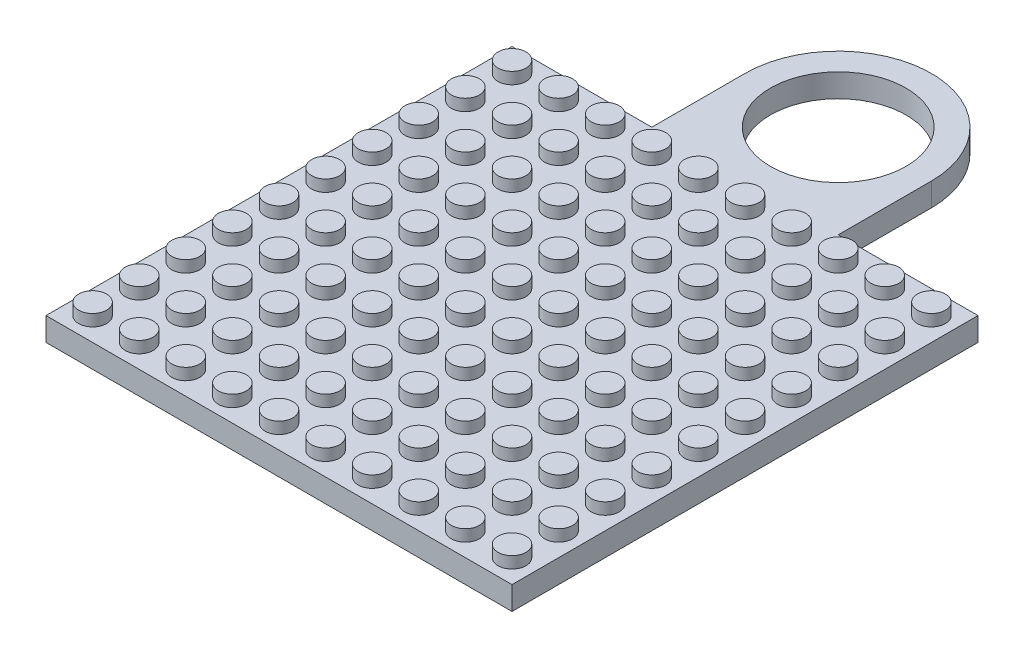
SolidWorks part; units mm, degrees
ref_plane "Front Plane" through (0, 0, 0) normal (0, 0, 1) x (1, 0, 0)
ref_plane "Top Plane" through (0, 0, 0) normal (0, 1, 0) x (1, 0, 0)
ref_plane "Right Plane" through (0, 0, 0) normal (1, 0, 0) x (0, 0, -1)
sketch "Sketch1" plane through (0, 0, 0) normal (0, 1, 0) x (1, 0, 0)
  line L1 (5, -5) -> (-5, -5)
  line L2 (5, -5) -> (5, 5)
  line L3 (5, 5) -> (-5, 5)
  line L4 (-5, -5) -> (-5, 5)
  line L5 (5, -5) -> (-5, 5) construction
  line L6 (5, 5) -> (-5, -5) construction
  point P0 (0, 0)
  dimension "D1" = 10
  dimension "D2" = 10
extrude "Plate" add sketch "Sketch1" along normal blind 0.5
sketch "Sketch2" plane through (0, 0.5, 0) normal (0, 1, 0) x (1, 0, 0)
  line L0 (-5, -5) -> (5, -5) construction
  line L1 (-5, 5) -> (-5, -5) construction
  circle A0 centre (-4.5, -4.5) radius 0.3
  dimension "D1" = 0.6
  dimension "D2" = 0.5
  dimension "D3" = 0.5
extrude "Rod" add sketch "Sketch2" along normal blind 0.25 contours A0
pattern_linear "LPattern1" count 10 spacing 1 along (1, 0, 0) count 10 spacing 1 along (0, 0, -1) of "Rod"
sketch "Sketch4" plane through (0, 0, 0) normal (0, 1, 0) x (1, 0, 0)
  line L5 (-2, 7) -> (-2, 5)
  line L6 (5, 5) -> (-5, 5) construction
  line L8 (-5, 5) -> (-5, -5) construction
  line L9 (-2, 5) -> (2, 5)
  line L10 (2, 5) -> (2, 7)
  arc A0 (-2, 7) -> (2, 7) centre (0, 7) cw
  point P0 (0, 7)
  dimension "D3" = 5
extrude "Boss-Extrude3" add sketch "Sketch4" along normal blind 0.5
sketch "Sketch5" plane through (0, 0.5, 0) normal (0, 1, 0) x (1, 0, 0)
  circle A0 centre (0, 7) radius 1.4559
extrude "Cut-Extrude1" cut sketch "Sketch5" against normal blind 1.5 and the other way blind 0.5
